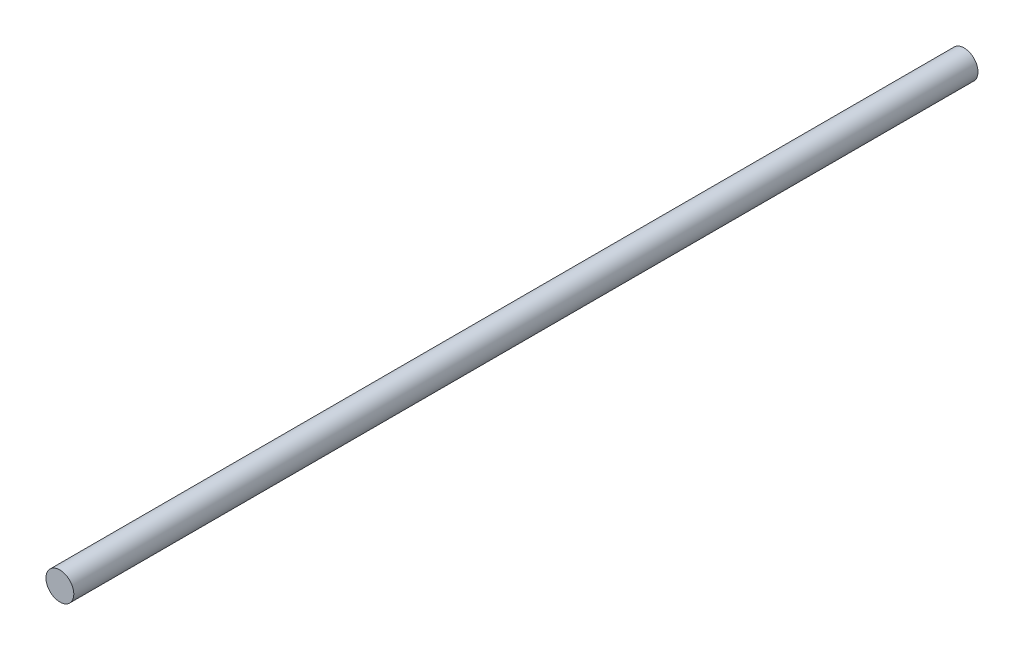
SolidWorks part; units mm, degrees
ref_plane "Front Plane" through (0, 0, 0) normal (0, 0, 1) x (1, 0, 0)
ref_plane "Top Plane" through (0, 0, 0) normal (0, 1, 0) x (1, 0, 0)
ref_plane "Right Plane" through (0, 0, 0) normal (1, 0, 0) x (0, 0, -1)
sketch "Sketch1" plane through (0, 0, 0) normal (0, 0, 1) x (1, 0, 0)
  circle A0 centre (0, 0) radius 5
  dimension "D1" = 10
extrude "Boss-Extrude1" add sketch "Sketch1" along normal blind 325
